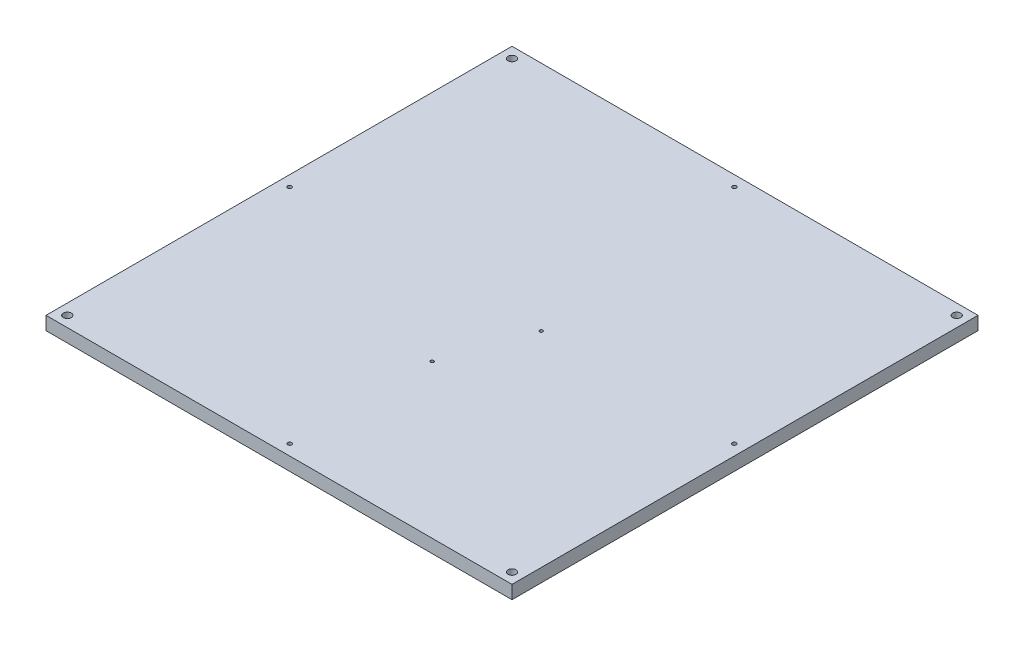
SolidWorks part; units mm, degrees
material "3003 Alloy"
ref_plane "Front Plane" through (0, 0, 0) normal (0, 0, 1) x (1, 0, 0)
ref_plane "Top Plane" through (0, 0, 0) normal (0, 1, 0) x (1, 0, 0)
ref_plane "Right Plane" through (0, 0, 0) normal (1, 0, 0) x (0, 0, -1)
sketch "Sketch1" plane through (0, 0, 0) normal (0, 1, 0) x (1, 0, 0)
  line L1 (-1000, -1000) -> (1000, -1000)
  line L2 (-1000, -1000) -> (-1000, 1000)
  line L3 (-1000, 1000) -> (1000, 1000)
  line L4 (1000, -1000) -> (1000, 1000)
  line L5 (-1000, -1000) -> (1000, 1000) construction
  line L6 (-1000, 1000) -> (1000, -1000) construction
  point P0 (0, 0)
  dimension "D1" = 2000
  dimension "D2" = 2000
extrude "Boss-Extrude1" add sketch "Sketch1" against normal blind 50
sketch "Sketch2" plane through (0, 0, 0) normal (0, 1, 0) x (1, 0, 0)
  circle A1 centre (0, -175) radius 6
  circle A3 centre (106, 129) radius 6
  dimension "D1" = 12
  dimension "D3" = 129
  dimension "D2" = 106
  dimension "D4" = 175
extrude "Cut-Extrude1" cut sketch "Sketch2" against normal blind 30
sketch "Sketch3" plane through (0, 0, 1000) normal (0, 0, 1) x (1, 0, 0)
  line L1 (-1000, 0) -> (1000, 0)
  line L2 (-1000, 0) -> (-1000, -50)
  line L3 (-1000, -50) -> (1000, -50)
  line L4 (1000, 0) -> (1000, -50)
extrude "Cut-Extrude2" cut sketch "Sketch3" against normal blind 250
sketch "Sketch4" plane through (-1000, 0, 0) normal (-1, 0, 0) x (0, 0, 1)
  line L1 (-1000, 0) -> (750, 0)
  line L2 (-1000, 0) -> (-1000, -50)
  line L3 (-1000, -50) -> (750, -50)
  line L4 (750, 0) -> (750, -50)
extrude "Cut-Extrude3" cut sketch "Sketch4" against normal blind 125
sketch "Sketch5" plane through (1000, 0, 0) normal (1, 0, 0) x (0, 0, -1)
  line L1 (-750, 0) -> (1000, 0)
  line L2 (-750, 0) -> (-750, -50)
  line L3 (-750, -50) -> (1000, -50)
  line L4 (1000, 0) -> (1000, -50)
extrude "Cut-Extrude4" cut sketch "Sketch5" against normal blind 125
sketch "Sketch6" plane through (0, 0, 0) normal (0, 1, 0) x (1, 0, 0)
  line L0 (-875, -750) -> (-875, 1000) construction
  line L1 (875, 1000) -> (-875, 1000) construction
  line L2 (875, 1000) -> (875, -750) construction
  line L3 (875, -750) -> (-875, -750) construction
  circle A0 centre (-835, -710) radius 15
  circle A1 centre (835, 960) radius 15
  circle A2 centre (835, -710) radius 15
  circle A3 centre (-835, 960) radius 15
  circle A4 centre (0, -710) radius 7.5
  circle A5 centre (0, 960) radius 7.5
  circle A6 centre (-835, 125) radius 7.5
  circle A7 centre (835, 125) radius 7.5
  point P25 (0, 0)
  point P26 (0, 0)
  point P27 (0, 0)
  dimension "D1" = 40
  dimension "D2" = 30
  dimension "D3" = 40
  dimension "D4" = 40
  dimension "D5" = 30
  dimension "D6" = 30
  dimension "D7" = 40
  dimension "D8" = 30
  dimension "D9" = 15
  dimension "D10" = 15
  dimension "D11" = 875
  dimension "D12" = 15
  dimension "D13" = 15
extrude "Cut-Extrude5" cut sketch "Sketch6" against normal blind 25
